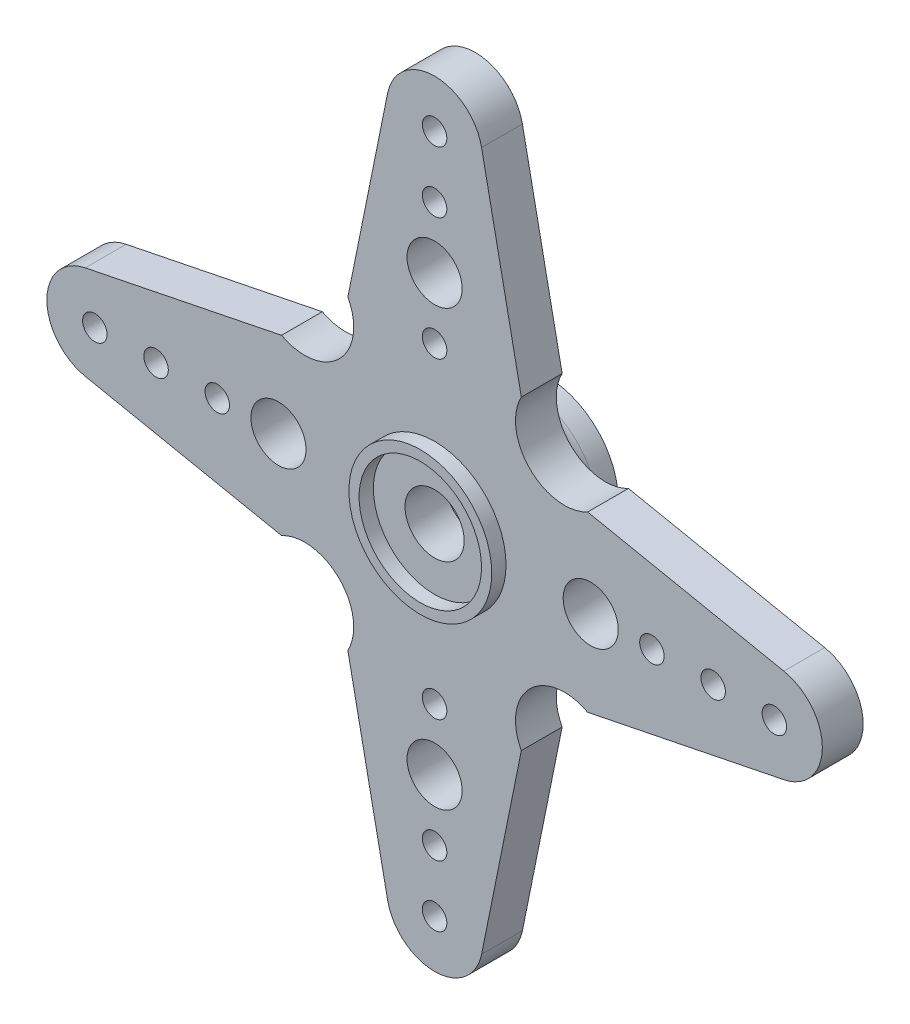
SolidWorks part; units mm, degrees
material "PP Kopolymer"
ref_plane "Ebene vorne" through (0, 0, 0) normal (0, 0, 1) x (1, 0, 0)
ref_plane "Ebene oben" through (0, 0, 0) normal (0, 1, 0) x (1, 0, 0)
ref_plane "Ebene rechts" through (0, 0, 0) normal (1, 0, 0) x (0, 0, -1)
sketch "Skizze1" plane through (0, 0, 0) normal (0, 0, 1) x (1, 0, 0)
  line L0 (0, -31.8089) -> (0, 35.3154) construction
  line L1 (-2.3033, 17.1163) -> (-4.25, 7.5)
  line L2 (2.3033, 17.1163) -> (4.25, 7.5)
  line L3 (17.1163, 2.3033) -> (7.5, 4.25)
  line L4 (17.1163, -2.3033) -> (7.5, -4.25)
  line L5 (-17.1163, 2.3033) -> (-7.5, 4.25)
  line L6 (2.3033, -17.1163) -> (4.25, -7.5)
  line L7 (0, 0) -> (6.364, -6.364) construction
  line L8 (0, 0) -> (6.364, 6.364) construction
  line L9 (-17.1163, -2.3033) -> (-7.5, -4.25)
  line L10 (-2.3033, -17.1163) -> (-4.25, -7.5)
  arc A0 (2.3033, 17.1163) -> (-2.3033, 17.1163) centre (0, 16.65) ccw
  arc A1 (17.1163, -2.3033) -> (17.1163, 2.3033) centre (16.65, 0) ccw
  arc A2 (-2.3033, -17.1163) -> (2.3033, -17.1163) centre (0, -16.65) ccw
  circle A3 centre (0, 0) radius 9 construction
  arc A4 (4.25, 7.5) -> (7.5, 4.25) centre (6.364, 6.364) ccw
  arc A5 (7.5, -4.25) -> (4.25, -7.5) centre (6.364, -6.364) ccw
  arc A6 (-4.25, 7.5) -> (-7.5, 4.25) centre (-6.364, 6.364) cw
  arc A7 (-17.1163, -2.3033) -> (-17.1163, 2.3033) centre (-16.65, 0) cw
  arc A8 (-7.5, -4.25) -> (-4.25, -7.5) centre (-6.364, -6.364) cw
  dimension "D1" = 4.7
  dimension "D2" = 4.7
  dimension "D3" = 4.7
  dimension "D5" = 19
  dimension "D11" = 11.5
  dimension "D13" = 18
  dimension "D14" = 90
  dimension "D4" = 19
  dimension "D6" = 19
  dimension "D7" = 4.25
  dimension "D8" = 8.5
  dimension "D16" = 45
extrude "Aufsatz-Linear austragen1" add sketch "Skizze1" along normal blind 2
hole_wizard "Ø1.2 (1.2) Durchmesser Bohrung1" positions "Skizze3" profile "Skizze2" hole size "Ø1.2" standard "DIN"
sketch "Skizze3" plane through (0, 0, 0) normal (0, 0, -1) x (-1, 0, 0)
  arc A0 (2.3033, 17.1163) -> (-2.3033, 17.1163) centre (0, 16.65) ccw construction
  arc A1 (17.1163, -2.3033) -> (17.1163, 2.3033) centre (16.65, 0) ccw construction
  point P0 (0, 16.65)
  point P2 (0, 10.65)
  point P4 (0, 7.65)
  point P9 (0, 13.65)
  point P19 (16.65, 0)
  point P21 (13.65, 0)
  point P23 (10.65, 0)
  point P25 (7.65, 0)
  dimension "D1" = 3
  dimension "D2" = 3
  dimension "D3" = 3
  dimension "D4" = 3
  dimension "D5" = 3
  dimension "D6" = 3
sketch "Skizze2" plane through (0, 16.65, 0) normal (1, 0, 0) x (0, 1, 0)
  line L0 (0, 0) -> (0, 10.3605)
  line L1 (0, 10.3605) -> (0.6, 10)
  line L2 (0.6, 10) -> (0.6, 0)
  line L5 (0.6, 0) -> (0, 0)
  line L10 (0, 10.3605) -> (-0.6, 10) construction
  line L11 (0, -6.35) -> (0, 107.95) construction
  dimension "Bohrerdurchmesser" = 1.2
  dimension "Bohrungstiefe" = 10
  dimension "Spitzenwinkel" = 118
mirror "Spiegeln1" about plane through (0, 0, 0) normal (1, 0, 0) of "Ø1.2 (1.2) Durchmesser Bohrung1"
mirror "Spiegeln2" about plane through (0, 0, 0) normal (0, 1, 0) of "Ø1.2 (1.2) Durchmesser Bohrung1"
sketch "Skizze4" plane through (0, 0, 0) normal (1, 0, 0) x (0, 0, -1)
  line L0 (-3.1105, 0) -> (6.3609, 0) construction
  line L1 (0, 5) -> (1, 5)
  line L2 (0, 2.3033) -> (0, 4.25) construction
  line L3 (3.5, 3.5) -> (3.5, 3)
  line L4 (3.5, 3) -> (0, 3)
  line L5 (0, -2.3033) -> (0, 2.3033) construction
  line L6 (2.5, 3.5) -> (3.5, 3.5)
  line L7 (-2, 3.5) -> (-2.7, 3.5)
  line L8 (-2, 2.3033) -> (-2, 4.25) construction
  line L9 (-2.7, 3.5) -> (-2.7, 3)
  line L10 (-2.7, 3) -> (-2, 3)
  line L11 (0, 3) -> (0, 5)
  line L12 (-2, 3) -> (-2, 3.5)
  arc A0 (1, 5) -> (2.5, 3.5) centre (2.5, 5) ccw
  dimension "D3" = 3.5
  dimension "D4" = 6
  dimension "D5" = 1.5
  dimension "D1" = 10
  dimension "D2" = 1
  dimension "D6" = 7
  dimension "D7" = 6
  dimension "D8" = 0.7
revolve "Rotation1" add sketch "Skizze4" angle 360 about L0
hole_wizard "Ø2.9 (2.9) Durchmesser Bohrung1" positions "Skizze6" profile "Skizze7" hole size "Ø2.9" standard "DIN" end condition through all
sketch "Skizze6" plane through (0, 0, 0) normal (0, 0, -1) x (-1, 0, 0)
  point P0 (0, 0)
sketch "Skizze7" plane through (0, 0, 0) normal (1, 0, 0) x (0, 1, 0)
  line L0 (0, 0) -> (0, 2.7)
  line L1 (0, 2.7) -> (1.45, 2.7)
  line L2 (1.45, 2.7) -> (1.45, 0)
  line L5 (1.45, 0) -> (0, 0)
  line L11 (0, -6.35) -> (0, 107.95) construction
  dimension "Bohrerdurchmesser" = 2.9
  dimension "Bohrungstiefe" = 2.7
hole_wizard "Ø2.7 (2.7) Diameter Hole1" positions "Sketch2" profile "Sketch1" hole size "Ø2.7" standard "DIN" end condition up to next
sketch "Sketch2" plane through (0, 0, 0) normal (0, 0, -1) x (-1, 0, 0)
  point P0 (-7.65, 0)
  point P3 (7.65, 0)
  point P13 (0, 10.65)
  point P16 (0, -10.65)
sketch "Sketch1" plane through (7.65, 0, 0) normal (1, 0, 0) x (0, 1, 0)
  line L0 (0, 0) -> (0, 2.7)
  line L1 (0, 2.7) -> (1.35, 2.7)
  line L2 (1.35, 2.7) -> (1.35, 0)
  line L5 (1.35, 0) -> (0, 0)
  line L11 (0, -6.35) -> (0, 107.95) construction
  dimension "Thru Hole Dia." = 2.7
  dimension "Thru Hole Depth" = 2.7
